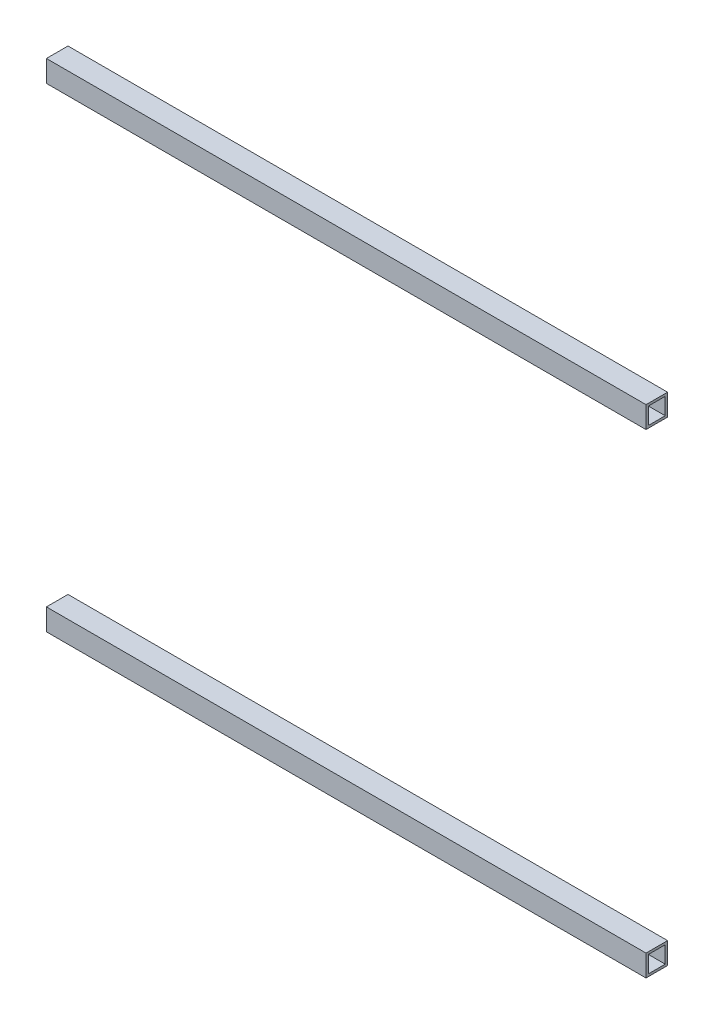
SolidWorks part; units mm, degrees
material "6061 Alloy"
ref_plane "Front Plane" through (0, 0, 0) normal (0, 0, 1) x (1, 0, 0)
ref_plane "Top Plane" through (0, 0, 0) normal (0, 1, 0) x (1, 0, 0)
ref_plane "Right Plane" through (0, 0, 0) normal (1, 0, 0) x (0, 0, -1)
sketch "Sketch1" plane through (0, 0, 0) normal (0, 0, 1) x (1, 0, 0)
  line L0 (0, 0) -> (529.05, 0)
  line L1 (0, 419.05) -> (529.05, 419.05)
  dimension "D1" = 529.05
  dimension "D2" = 419.05
other "Al tube square AL TUBE 0.75 SQR X 0.083 WALL(1)"
ref_plane "Plane1" through (0, 419.05, 0) normal (1, 0, 0) x (0, 1, 0)
sketch "Sketch11" plane through (0, 419.05, 0) normal (1, 0, 0) x (0, 1, 0)
  line L0 (-7.4168, -7.4168) -> (-7.4168, 7.4168)
  line L1 (7.4168, 7.4168) -> (-7.4168, 7.4168)
  line L2 (7.4168, 7.4168) -> (7.4168, -7.4168)
  line L3 (-7.4168, -7.4168) -> (7.4168, -7.4168)
  line L4 (-9.525, -9.525) -> (9.525, -9.525)
  line L5 (-9.525, -9.525) -> (-9.525, 9.525)
  line L6 (9.525, 9.525) -> (-9.525, 9.525)
  line L7 (9.525, 9.525) -> (9.525, -9.525)
  line L8 (0, -7.4168) -> (0, -9.525) construction
  line L9 (0, -7.4168) -> (0, 7.4168) construction
  line L10 (0, 7.4168) -> (0, 9.525) construction
  line L11 (9.525, 0) -> (7.4168, 0) construction
  line L12 (7.4168, 0) -> (-7.4168, 0) construction
  line L13 (-7.4168, 0) -> (-9.525, 0) construction
  point P14 (0, 0)
  point P17 (0, 0)
  dimension "Thickness" = 2.1082
  dimension "V_leg" = 19.05
  dimension "H_leg" = 19.05
